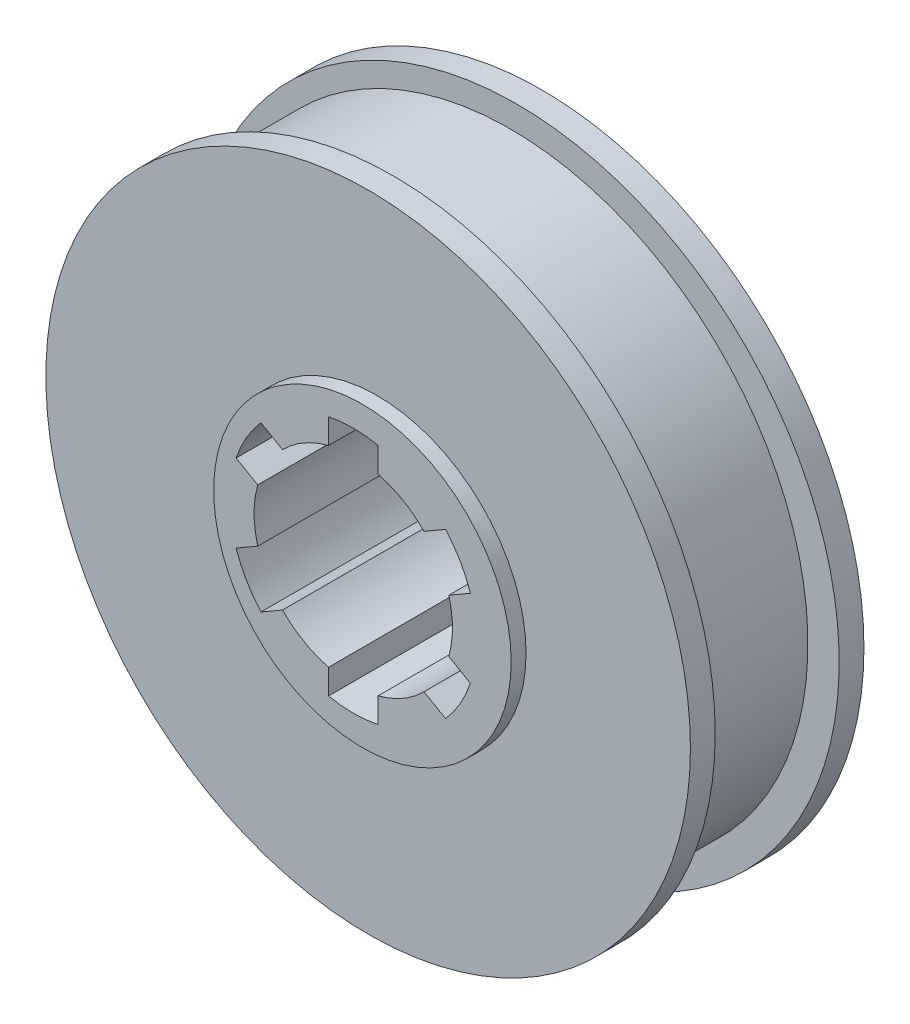
SolidWorks part; units mm, degrees
ref_plane "Front Plane" through (0, 0, 0) normal (0, 0, 1) x (1, 0, 0)
ref_plane "Top Plane" through (0, 0, 0) normal (0, 1, 0) x (1, 0, 0)
ref_plane "Right Plane" through (0, 0, 0) normal (1, 0, 0) x (0, 0, -1)
sketch "Sketch1" plane through (0, 0, 0) normal (0, 0, 1) x (1, 0, 0)
  line L0 (0.1299, 0) -> (0.1299, 4.001) construction
  line L1 (0.1299, 3.5548) -> (0.1299, 0.627) construction
  line L3 (-0.3701, 2.4393) -> (-0.3701, 0.627)
  line L4 (-0.3701, 0.627) -> (0.6299, 0.627)
  line L5 (0.6299, 2.4393) -> (0.6299, 0.627)
  line L6 (1.9924, 1.6527) -> (0.4229, 0.7465)
  line L8 (2.4924, 0.7866) -> (0.9229, -0.1195)
  line L9 (0.4229, 0.7465) -> (0.9229, -0.1195)
  line L10 (2.4924, -0.7866) -> (0.9229, 0.1195)
  line L12 (1.9924, -1.6527) -> (0.4229, -0.7465)
  line L13 (0.9229, 0.1195) -> (0.4229, -0.7465)
  line L14 (0.6299, -3.5481) -> (0.6299, -0.627)
  line L15 (0.6299, -3.5481) -> (-0.3701, -3.5481)
  line L16 (-0.3701, -3.5481) -> (-0.3701, -0.627)
  line L17 (0.6299, -0.627) -> (-0.3701, -0.627)
  line L18 (-1.7325, -1.6527) -> (-0.163, -0.7465)
  line L20 (-2.2325, -0.7866) -> (-0.663, 0.1195)
  line L21 (-0.163, -0.7465) -> (-0.663, 0.1195)
  line L22 (-2.2325, 0.7866) -> (-0.663, -0.1195)
  line L24 (-1.3331, -0.3309) -> (-2.0026, -0.7174) construction
  line L25 (-1.5576, -1.4882) -> (-0.8881, -1.1016) construction
  line L26 (-0.3151, -1.4325) -> (-0.3151, -2.2056) construction
  line L27 (0.5749, -2.2056) -> (0.5749, -1.4325) construction
  line L28 (1.148, -1.1016) -> (1.8175, -1.4882) construction
  line L29 (2.2625, -0.7174) -> (1.593, -0.3309) construction
  line L30 (1.593, 0.3309) -> (2.2625, 0.7174) construction
  line L31 (1.8175, 1.4882) -> (1.148, 1.1016) construction
  line L32 (0.5749, 1.4325) -> (0.5749, 2.2056) construction
  line L33 (-0.3151, 2.2056) -> (-0.3151, 1.4325) construction
  line L34 (-0.8881, 1.1016) -> (-1.5576, 1.4882) construction
  line L35 (-2.0026, 0.7174) -> (-1.3331, 0.3309) construction
  line L36 (-1.7325, 1.6527) -> (-0.163, 0.7465)
  line L37 (-0.663, -0.1195) -> (-0.163, 0.7465)
  circle A0 centre (0.1299, 0) radius 6.5
  circle A1 centre (0.1299, 0) radius 2
  circle A2 centre (0.1299, 0) radius 2.49
  arc A24 (-1.3331, 0.3309) -> (-1.3331, -0.3309) centre (0.1299, 0) ccw construction
  arc A25 (-2.0026, -0.7174) -> (-1.5576, -1.4882) centre (0.1299, 0) ccw construction
  arc A26 (-0.8881, -1.1016) -> (-0.3151, -1.4325) centre (0.1299, 0) ccw construction
  arc A27 (-0.3151, -2.2056) -> (0.5749, -2.2056) centre (0.1299, 0) ccw construction
  arc A28 (0.5749, -1.4325) -> (1.148, -1.1016) centre (0.1299, 0) ccw construction
  arc A29 (1.8175, -1.4882) -> (2.2625, -0.7174) centre (0.1299, 0) ccw construction
  arc A30 (1.593, -0.3309) -> (1.593, 0.3309) centre (0.1299, 0) ccw construction
  arc A31 (2.2625, 0.7174) -> (1.8175, 1.4882) centre (0.1299, 0) ccw construction
  arc A32 (1.148, 1.1016) -> (0.5749, 1.4325) centre (0.1299, 0) ccw construction
  arc A33 (0.5749, 2.2056) -> (-0.3151, 2.2056) centre (0.1299, 0) ccw construction
  arc A34 (-0.3151, 1.4325) -> (-0.8881, 1.1016) centre (0.1299, 0) ccw construction
  arc A35 (-1.5576, 1.4882) -> (-2.0026, 0.7174) centre (0.1299, 0) ccw construction
  point P69 (0.1299, 0)
  dimension "D1" = 13
  dimension "D2" = 4
  dimension "D3" = 4.98
  dimension "D4" = 6
  dimension "D5" = 1
extrude "Boss-Extrude1" add sketch "Sketch1" along normal blind 3.5 contours A0 A2 L14 L15 L16 | A2 L16 L15 L14 | L18 A2 L16 A1 | L14 A2 L12 A1 | L10 A2 L8 A1 | L6 A2 L5 A1 | L3 A2 L36 A1 | L22 A2 L20 A1 | A34 L34 A35 L35 A24 L24 A25 L25 A26 L26 A27 L27 A28 L28 A29 L29 A30 L30 A31 L31 A32 L32 A33 L33
sketch "Sketch3" plane through (0, 0, 3.5) normal (0, 0, 1) x (1, 0, 0)
  circle A0 centre (0.3149, 0) radius 3
  dimension "D1" = 6
extrude "Boss-Extrude2" add sketch "Sketch3" along normal blind 0.3
ref_plane "Plane1" through (0, 0, 0.5) normal (0, 0, -1) x (-1, 0, 0)
sketch "Sketch4" plane through (0, 0, 0.5) normal (0, 0, -1) x (-1, 0, 0)
  circle A0 centre (0, 0) radius 6
  circle A1 centre (-0.1299, 0) radius 6.5
  circle A2 centre (-0.1299, 0) radius 6.5
  dimension "D1" = 0
extrude "Cut-Extrude1" cut sketch "Sketch4" against normal offset from surface (2.5 mm away) 0.5 up to face at (6.6299, 0, 3.5)
